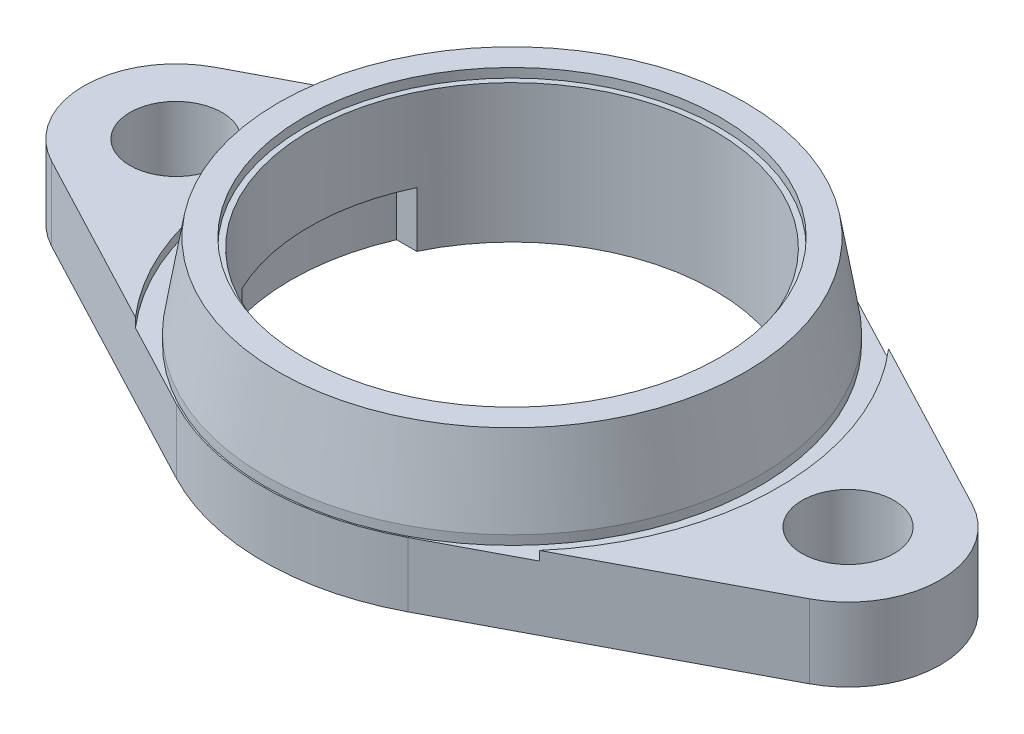
SolidWorks part; units mm, degrees
material "Zinc AC41A Alloy, As Cast"
ref_plane "Front Plane" through (0, 0, 0) normal (0, 0, 1) x (1, 0, 0)
ref_plane "Top Plane" through (0, 0, 0) normal (0, 1, 0) x (1, 0, 0)
ref_plane "Right Plane" through (0, 0, 0) normal (1, 0, 0) x (0, 0, -1)
sketch "Sketch1" plane through (0, 0, 0) normal (0, 1, 0) x (1, 0, 0)
  line L0 (-18.25, 0) -> (0, 0) construction
  line L1 (0, 0) -> (18.25, 0) construction
  line L2 (20.5788, 4.4246) -> (6.2877, 11.9463)
  line L3 (-20.5788, 4.4246) -> (-6.2877, 11.9463)
  line L4 (-20.5788, -4.4246) -> (-6.2877, -11.9463)
  line L5 (6.2877, -11.9463) -> (20.5788, -4.4246)
  circle A0 centre (-18.25, 0) radius 2.5 construction
  circle A1 centre (18.25, 0) radius 2.5 construction
  circle A2 centre (0, 0) radius 11
  arc A3 (6.2877, 11.9463) -> (-6.2877, 11.9463) centre (0, 0) ccw
  arc A4 (-20.5788, 4.4246) -> (-20.5788, -4.4246) centre (-18.25, 0) ccw
  arc A5 (20.5788, -4.4246) -> (20.5788, 4.4246) centre (18.25, 0) ccw
  arc A6 (-6.2877, -11.9463) -> (6.2877, -11.9463) centre (0, 0) ccw
  dimension "D1" = 27
  dimension "D2" = 22
  dimension "D3" = 10
  dimension "D4" = 5
  dimension "D5" = 36.5
extrude "Flange" add sketch "Sketch1" along normal blind 4
sketch "Sketch2" plane through (0, 0, 0) normal (0, 0, 1) x (1, 0, 0)
  line L0 (-13.425, 4) -> (-12.675, 8.5)
  line L1 (-12.675, 8.5) -> (-11.3, 8.5)
  line L2 (-11.3, 8.5) -> (-11.3, 8)
  line L3 (-11.3, 8) -> (-11, 8)
  line L4 (-11, 8) -> (-11, 4)
  line L5 (-11, 4) -> (-13.425, 4)
  line L6 (0, 0) -> (0, 4) construction
  line L7 (0, 4) -> (-11, 4) construction
  line L8 (11, 4) -> (-11, 4) construction
  dimension "D1" = 4.5
  dimension "D2" = 22
  dimension "D3" = 26.85
  dimension "D4" = 25.35
  dimension "D5" = 0.5
  dimension "D6" = 0.3
revolve "Bearing Seat" add sketch "Sketch2" angle 360 about L6
sketch "Sketch3" plane through (0, 4, 0) normal (0, 1, 0) x (1, 0, 0)
  line L4 (20.5788, 4.4246) -> (6.2877, 11.9463)
  line L5 (-6.2877, 11.9463) -> (-20.5788, 4.4246)
  line L6 (-20.5788, -4.4246) -> (-6.2877, -11.9463)
  line L7 (6.2877, -11.9463) -> (20.5788, -4.4246)
  line L8 (10.9702, 9.4818) -> (6.2877, 11.9463)
  line L9 (-6.2877, 11.9463) -> (-10.9702, 9.4818)
  line L10 (-10.9702, -9.4818) -> (-6.2877, -11.9463)
  line L11 (6.2877, -11.9463) -> (10.9702, -9.4818)
  arc A0 (-10.9702, 9.4818) -> (-10.9702, -9.4818) centre (0, 0) ccw
  circle A2 centre (0, 0) radius 13.425 construction
  arc A3 (10.9702, -9.4818) -> (10.9702, 9.4818) centre (0, 0) ccw
  arc A4 (20.5788, -4.4246) -> (20.5788, 4.4246) centre (18.25, 0) ccw
  arc A5 (6.2877, 11.9463) -> (-6.2877, 11.9463) centre (0, 0) ccw
  arc A6 (-20.5788, 4.4246) -> (-20.5788, -4.4246) centre (-18.25, 0) ccw
  arc A7 (-6.2877, -11.9463) -> (6.2877, -11.9463) centre (0, 0) ccw
  circle A8 centre (0, 0) radius 13.425
  arc A9 (-6.2877, -11.9463) -> (6.2877, -11.9463) centre (0, 0) ccw construction
  arc A10 (-6.2877, -11.9463) -> (6.2877, -11.9463) centre (0, 0) ccw
  arc A11 (6.2877, 11.9463) -> (-6.2877, 11.9463) centre (0, 0) ccw construction
  arc A12 (6.2877, 11.9463) -> (-6.2877, 11.9463) centre (0, 0) ccw
  dimension "D2" = 29
  dimension "D1" = 0
extrude "Top Recess" cut sketch "Sketch3" against normal blind 0.5
sketch "Sketch5" plane through (0, 0, 0) normal (0, -1, 0) x (1, 0, 0)
  line L0 (17.0094, 4.3256) -> (5.4726, 10.3977)
  line L1 (-5.4726, 10.3977) -> (-17.0094, 4.3256)
  line L2 (-17.0094, -4.3256) -> (-5.4726, -10.3977)
  line L3 (5.4726, -10.3977) -> (17.0094, -4.3256)
  line L4 (20.5788, 4.4246) -> (6.2877, 11.9463)
  line L5 (-6.2877, 11.9463) -> (-20.5788, 4.4246)
  line L6 (-20.5788, -4.4246) -> (-6.2877, -11.9463)
  line L7 (6.2877, -11.9463) -> (20.5788, -4.4246)
  line L8 (20.5788, 4.4246) -> (6.2877, 11.9463) construction
  line L9 (-6.2877, 11.9463) -> (-20.5788, 4.4246) construction
  line L10 (-20.5788, -4.4246) -> (-6.2877, -11.9463) construction
  line L11 (6.2877, -11.9463) -> (20.5788, -4.4246) construction
  line L13 (-5.4726, 10.3977) -> (-19.7637, 2.876) construction
  line L14 (-19.7637, -2.876) -> (-5.4726, -10.3977) construction
  line L15 (5.4726, -10.3977) -> (19.7637, -2.876) construction
  line L16 (19.7637, 2.876) -> (5.4726, 10.3977) construction
  arc A0 (5.4726, 10.3977) -> (-5.4726, 10.3977) centre (0, 0) ccw
  arc A2 (-5.4726, -10.3977) -> (5.4726, -10.3977) centre (0, 0) ccw
  arc A4 (20.5788, -4.4246) -> (20.5788, 4.4246) centre (18.25, 0) ccw
  arc A5 (6.2877, 11.9463) -> (-6.2877, 11.9463) centre (0, 0) ccw
  arc A6 (-20.5788, 4.4246) -> (-20.5788, -4.4246) centre (-18.25, 0) ccw
  arc A7 (-6.2877, -11.9463) -> (6.2877, -11.9463) centre (0, 0) ccw
  arc A8 (20.5788, -4.4246) -> (20.5788, 4.4246) centre (18.25, 0) ccw construction
  arc A9 (6.2877, 11.9463) -> (-6.2877, 11.9463) centre (0, 0) ccw construction
  arc A10 (-20.5788, 4.4246) -> (-20.5788, -4.4246) centre (-18.25, 0) ccw construction
  arc A11 (-6.2877, -11.9463) -> (6.2877, -11.9463) centre (0, 0) ccw construction
  arc A12 (-17.0094, -4.3256) -> (-17.0094, 4.3256) centre (-18.25, 0) ccw
  arc A13 (17.0094, 4.3256) -> (17.0094, -4.3256) centre (18.25, 0) ccw
  arc A14 (-19.7637, 2.876) -> (-19.7637, -2.876) centre (-18.25, 0) ccw construction
  arc A15 (19.7637, -2.876) -> (19.7637, 2.876) centre (18.25, 0) ccw construction
  dimension "D3" = 9
  dimension "D1" = 0
  dimension "D2" = 1.75
extrude "Bottom Recess 1" cut sketch "Sketch5" against normal blind 0.5
sketch "Sketch6" plane through (0, 0.5, 0) normal (0, -1, 0) x (1, 0, 0)
  line L0 (-11.0199, 4.75) -> (11.0199, 4.75)
  line L1 (-11.0199, -4.75) -> (11.0199, -4.75)
  circle A0 centre (0, 0) radius 11 construction
  circle A1 centre (0, 0) radius 11 construction
  arc A2 (11.0199, -4.75) -> (11.0199, 4.75) centre (0, 0) ccw
  arc A3 (-11.0199, 4.75) -> (-11.0199, -4.75) centre (0, 0) ccw
  circle A4 centre (0, 0) radius 12 construction
  point P9 (12, 0)
  dimension "D2" = 9.5
  dimension "D1" = 1
extrude "Bottom Recess 2" cut sketch "Sketch6" against normal blind 3
hole_wizard "Mounting Hole (M5x0.8)" positions "Sketch10" profile "Sketch9" tap size "M6x1.0" standard "ANSI Metric" end condition through all
sketch "Sketch10" plane through (0, 4, 0) normal (0, 1, 0) x (1, 0, 0)
  point P0 (18.25, 0)
  point P3 (-18.25, 0)
sketch "Sketch9" plane through (18.25, 4, 0) normal (1, 0, 0) x (0, 0, 1)
  line L0 (0, 0) -> (0, 4)
  line L1 (0, 4) -> (2.5, 4)
  line L2 (2.5, 4) -> (2.5, 0)
  line L5 (2.5, 0) -> (0, 0)
  line L11 (0, -6.35) -> (0, 107.95) construction
  dimension "Thru Tap Drill Dia." = 5
  dimension "Thru Tap Drill Depth" = 4
cosmetic thread "Hole Thread3" parameters "D2"=6
cosmetic thread "Hole Thread4" parameters "D2"=6
